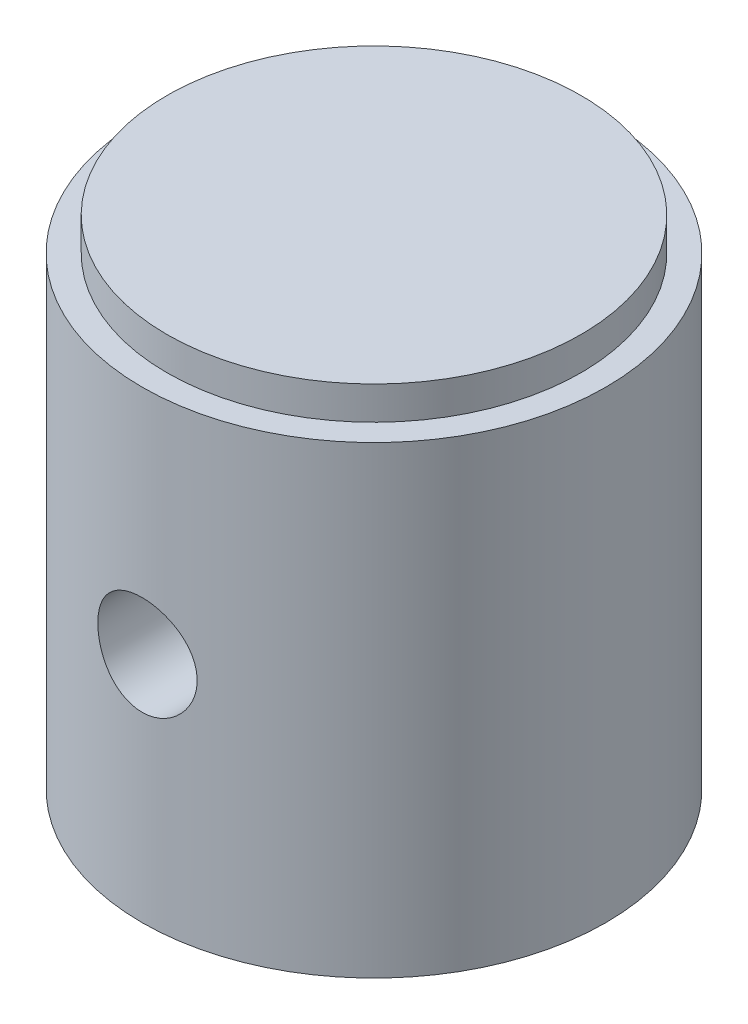
SolidWorks part; units mm, degrees
ref_plane "Front Plane" through (0, 0, 0) normal (0, 0, 1) x (1, 0, 0)
ref_plane "Top Plane" through (0, 0, 0) normal (0, 1, 0) x (1, 0, 0)
ref_plane "Right Plane" through (0, 0, 0) normal (1, 0, 0) x (0, 0, -1)
sketch "Sketch1" plane through (0, 0, 0) normal (0, 0, 1) x (1, 0, 0)
  line L0 (0, 19.3671) -> (0, -8.4115) construction
  line L1 (-7, 0) -> (-6.25, 0)
  line L2 (-6.25, 0) -> (-4.75, 4.1212)
  line L3 (-4.75, 4.1212) -> (-4.75, 11)
  line L4 (-4.75, 11) -> (0, 13.8541)
  line L5 (-7, 0) -> (-7, 14)
  line L6 (-7, 14) -> (-6.25, 14)
  line L7 (-6.25, 14) -> (-6.25, 15)
  line L8 (-6.25, 15) -> (0, 15)
  line L9 (-8.6959, 11) -> (6.171, 11) construction
  line L10 (0, 15) -> (0, 13.8541)
  dimension "D1" = 6.25
  dimension "D2" = 7
  dimension "D3" = 11
  dimension "D4" = 15
  dimension "D5" = 6.25
  dimension "D6" = 1
  dimension "D7" = 4.75
  dimension "D8" = 20
  dimension "D9" = 59
revolve "Revolve1" add sketch "Sketch1" angle 360 about L0
sketch "Sketch2" plane through (0, 0, 0) normal (0, 0, 1) x (1, 0, 0)
  line L0 (-7, 0) -> (7, 0) construction
  circle A0 centre (0, 7) radius 1.5
  point P4 (0, 0)
  dimension "D1" = 3
  dimension "D2" = 7
extrude "Cut-Extrude1" cut sketch "Sketch2" against normal through all both and the other way through all
